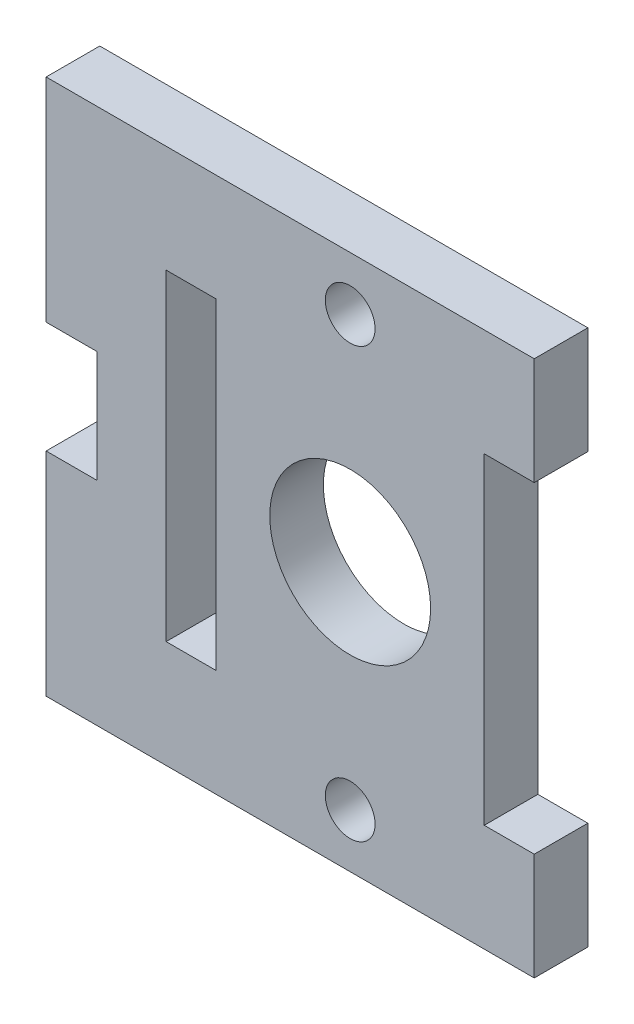
SolidWorks part; units mm, degrees
ref_plane "Front Plane" through (0, 0, 0) normal (0, 0, 1) x (1, 0, 0)
ref_plane "Top Plane" through (0, 0, 0) normal (0, 1, 0) x (1, 0, 0)
ref_plane "Right Plane" through (0, 0, 0) normal (1, 0, 0) x (0, 0, -1)
sketch "Sketch1" plane through (0, 0, 0) normal (0, 0, 1) x (1, 0, 0)
  line L0 (7.9375, -3.175) -> (10.8966, -3.175)
  line L1 (-10.8966, 3.175) -> (10.8966, 3.175)
  line L2 (-10.8966, 3.175) -> (-10.8966, -3.175)
  line L3 (-10.8966, -3.175) -> (-7.9375, -3.175)
  line L4 (10.8966, 3.175) -> (10.8966, -3.175)
  line L5 (-10.8966, 3.175) -> (10.8966, -3.175) construction
  line L6 (-10.8966, -3.175) -> (10.8966, 3.175) construction
  line L7 (-12.7, -12.7) -> (12.7, -12.7) construction
  line L8 (-7.9375, -3.175) -> (-7.9375, -22.225)
  line L9 (0, -3.9078) -> (0, -8.5431) construction
  line L10 (7.9375, -3.175) -> (7.9375, -22.225)
  line L11 (0, -21.4922) -> (0, -16.8569) construction
  line L12 (-10.8966, -22.225) -> (10.8966, -28.575) construction
  line L13 (-10.8966, -28.575) -> (10.8966, -22.225) construction
  line L14 (10.8966, -28.575) -> (10.8966, -22.225)
  line L15 (-10.8966, -22.225) -> (-7.9375, -22.225)
  line L16 (-10.8966, -28.575) -> (-10.8966, -22.225)
  line L17 (-10.8966, -28.575) -> (10.8966, -28.575)
  line L18 (7.9375, -22.225) -> (10.8966, -22.225)
  point P0 (0, 0)
  point P8 (0, -25.4)
  point P21 (7.9375, -12.7)
  point P22 (-7.9375, -12.7)
  dimension "D1" = 6.35
  dimension "D2" = 2.9591
  dimension "D3" = 15.875
  dimension "D5" = 15.875
extrude "Boss-Extrude1" add sketch "Sketch1" along normal blind 3.175
hole_wizard "#4 Clearance Hole1" positions "Sketch3" profile "Sketch2" hole size "#4" standard "ANSI Inch"
sketch "Sketch3" plane through (0, 0, 3.175) normal (0, 0, 1) x (1, 0, 0)
  point P0 (0, 0)
  point P5 (0, -25.4)
sketch "Sketch2" plane through (0, 0, 3.175) normal (1, 0, 0) x (0, -1, 0)
  line L0 (0, 0) -> (0, 4.1872)
  line L1 (0, 4.1872) -> (1.4732, 3.302)
  line L2 (1.4732, 3.302) -> (1.4732, 0)
  line L5 (1.4732, 0) -> (0, 0)
  line L10 (0, 4.1872) -> (-1.4732, 3.302) construction
  line L11 (0, -6.35) -> (0, 107.95) construction
  dimension "Hole Dia." = 2.9464
  dimension "Hole Depth" = 3.302
  dimension "Drill Angle" = 118
sketch "Sketch4" plane through (0, 0, 3.175) normal (0, 0, 1) x (1, 0, 0)
  line L0 (-7.9375, -3.175) -> (-7.9375, -22.225) construction
  circle A0 centre (0, -12.7) radius 4.7625
  point P4 (-7.9375, -12.7)
  dimension "D1" = 9.525
extrude "Cut-Extrude1" cut sketch "Sketch4" against normal up to next contours A0
sketch "Sketch5" plane through (0, 0, 3.175) normal (0, 0, 1) x (1, 0, 0)
  line L0 (-10.8966, -3.175) -> (-10.8966, -22.225)
  line L1 (-10.8966, 3.175) -> (-18, 3.175)
  line L2 (-18, 3.175) -> (-18, -9.398)
  line L3 (-18, -9.398) -> (-15, -9.398)
  line L4 (-15, -9.398) -> (-15, -16.002)
  line L5 (0, -12.7) -> (-24.0905, -12.7) construction
  line L6 (-18, -16.002) -> (-15, -16.002)
  line L7 (-18, -28.575) -> (-18, -16.002)
  line L8 (-10.8966, -28.575) -> (-18, -28.575)
  line L9 (-10.8966, 3.175) -> (-10.8966, -3.175)
  line L10 (-10.8966, -28.575) -> (-10.8966, -22.225)
  circle A0 centre (0, -12.7) radius 4.7625 construction
  dimension "D1" = 6.604
  dimension "D2" = 15
  dimension "D3" = 18
extrude "Boss-Extrude2" add sketch "Sketch5" against normal up to surface (3.175 mm away) up to face at (4.7625, -12.7, 0)
